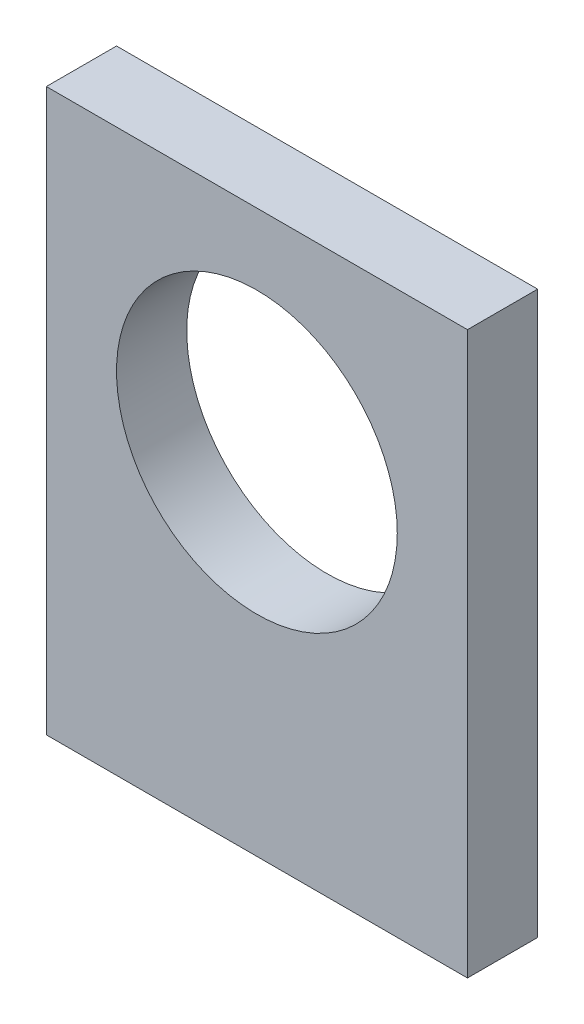
SolidWorks part; units mm, degrees
ref_plane "Front Plane" through (0, 0, 0) normal (0, 0, 1) x (1, 0, 0)
ref_plane "Top Plane" through (0, 0, 0) normal (0, 1, 0) x (1, 0, 0)
ref_plane "Right Plane" through (0, 0, 0) normal (1, 0, 0) x (0, 0, -1)
sketch "Sketch1" plane through (0, 0, 0) normal (0, 0, 1) x (1, 0, 0)
  line L1 (-15, -20) -> (15, -20)
  line L2 (-15, -20) -> (-15, 20)
  line L3 (-15, 20) -> (15, 20)
  line L4 (15, -20) -> (15, 20)
  line L5 (-15, -20) -> (15, 20) construction
  line L6 (-15, 20) -> (15, -20) construction
  circle A0 centre (0, 4.9388) radius 10
  point P0 (0, 0)
  point P6 (0, 4.9388)
  point P10 (0, 0)
extrude "Boss-Extrude1" add sketch "Sketch1" along normal blind 5
